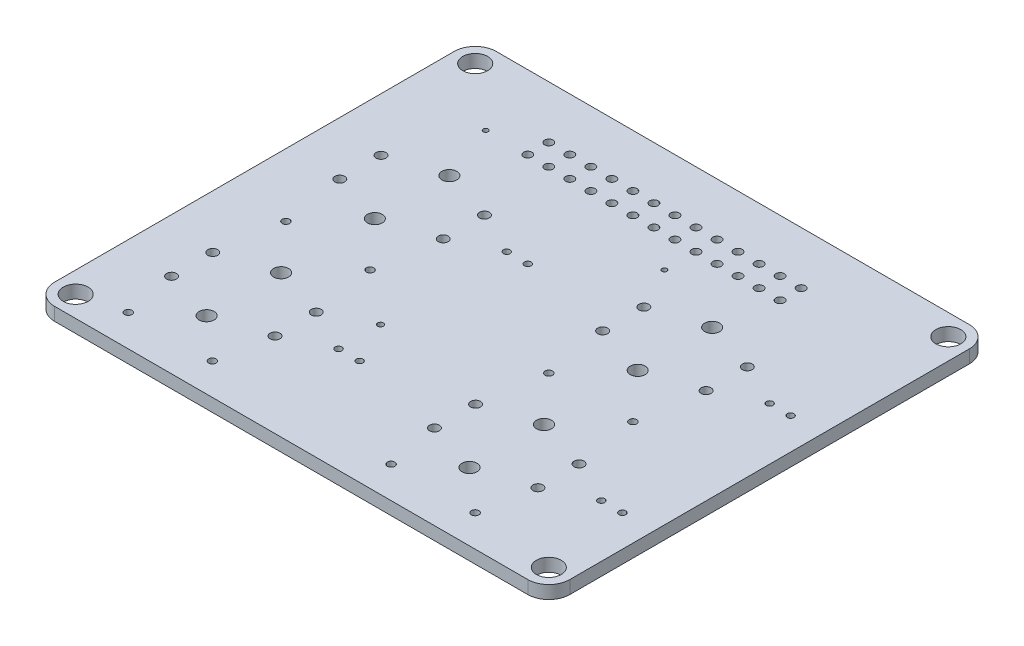
SolidWorks part; units mm, degrees
ref_plane "Front Plane" through (0, 0, 0) normal (0, 0, 1) x (1, 0, 0)
ref_plane "Top Plane" through (0, 0, 0) normal (0, 1, 0) x (1, 0, 0)
ref_plane "Right Plane" through (0, 0, 0) normal (1, 0, 0) x (0, 0, -1)
sketch "Sketch1" plane through (0, 0, 0) normal (0, 1, 0) x (1, 0, 0)
  line L1 (-28.575, 26.67) -> (28.575, 26.67)
  line L2 (-31.115, 24.13) -> (-31.115, -24.13)
  line L3 (-28.575, -26.67) -> (28.575, -26.67)
  line L4 (31.115, 24.13) -> (31.115, -24.13)
  line L5 (-31.115, 26.67) -> (31.115, -26.67) construction
  line L6 (-31.115, -26.67) -> (31.115, 26.67) construction
  arc A4 (28.575, 26.67) -> (31.115, 24.13) centre (28.575, 24.13) cw
  arc A5 (28.575, -26.67) -> (31.115, -24.13) centre (28.575, -24.13) ccw
  arc A6 (-31.115, -24.13) -> (-28.575, -26.67) centre (-28.575, -24.13) ccw
  arc A7 (-28.575, 26.67) -> (-31.115, 24.13) centre (-28.575, 24.13) ccw
  point P0 (0, 0)
  dimension "D15" = 2.54
  dimension "D1" = 62.23
  dimension "D2" = 53.34
extrude "Boss-Extrude1" add sketch "Sketch1" along normal blind 1.5748
sketch "Sketch2" plane through (0, 1.5748, 0) normal (0, 1, 0) x (1, 0, 0)
  line L0 (-28.575, 24.13) -> (-28.575, -24.13) construction
  line L1 (-28.575, -24.13) -> (28.575, -24.13) construction
  line L2 (28.575, -24.13) -> (28.575, 24.13) construction
  line L3 (28.575, 24.13) -> (-28.575, 24.13) construction
  line L4 (28.575, 26.67) -> (-28.575, 26.67) construction
  line L5 (-31.115, 24.13) -> (-31.115, -24.13) construction
  line L6 (31.115, -24.13) -> (31.115, 24.13) construction
  line L7 (-28.575, -26.67) -> (28.575, -26.67) construction
  line L8 (-24.6634, -11.4808) -> (-12.1666, -16.4592) construction
  line L9 (-24.6634, -16.4592) -> (-12.1666, -16.4592) construction
  line L10 (-24.6634, -16.4592) -> (-24.6634, -11.4808) construction
  line L11 (-24.6634, -11.4808) -> (-12.1666, -11.4808) construction
  line L12 (-12.1666, -16.4592) -> (-12.1666, -11.4808) construction
  line L13 (-12.1666, -11.4808) -> (-24.6634, -16.4592) construction
  line L14 (-18.415, -13.97) -> (-18.415, -22.86) construction
  line L15 (-13.335, -22.86) -> (-23.495, -22.86) construction
  line L16 (-18.415, -13.97) -> (-4.445, -13.97) construction
  line L17 (-18.415, -13.97) -> (-18.415, -9.4742) construction
  line L18 (7.0866, -11.4808) -> (19.5834, -16.4592) construction
  line L19 (7.0866, -16.4592) -> (19.5834, -16.4592) construction
  line L20 (7.0866, -16.4592) -> (7.0866, -11.4808) construction
  line L21 (7.0866, -11.4808) -> (19.5834, -11.4808) construction
  line L22 (19.5834, -16.4592) -> (19.5834, -11.4808) construction
  line L23 (19.5834, -11.4808) -> (7.0866, -16.4592) construction
  line L24 (13.335, -13.97) -> (13.335, -22.86) construction
  line L25 (13.335, -13.97) -> (27.305, -13.97) construction
  line L26 (13.335, -13.97) -> (13.335, -9.4742) construction
  line L27 (7.0866, 8.8392) -> (19.5834, 3.8608) construction
  line L28 (7.0866, 3.8608) -> (19.5834, 3.8608) construction
  line L29 (7.0866, 3.8608) -> (7.0866, 8.8392) construction
  line L30 (7.0866, 8.8392) -> (19.5834, 8.8392) construction
  line L31 (19.5834, 3.8608) -> (19.5834, 8.8392) construction
  line L32 (19.5834, 8.8392) -> (7.0866, 3.8608) construction
  line L33 (13.335, 6.35) -> (13.335, -2.54) construction
  line L34 (13.335, 6.35) -> (27.305, 6.35) construction
  line L35 (13.335, 6.35) -> (13.335, 10.8458) construction
  line L36 (-24.6634, 8.8392) -> (-12.1666, 3.8608) construction
  line L37 (-24.6634, 3.8608) -> (-12.1666, 3.8608) construction
  line L38 (-24.6634, 3.8608) -> (-24.6634, 8.8392) construction
  line L39 (-24.6634, 8.8392) -> (-12.1666, 8.8392) construction
  line L40 (-12.1666, 3.8608) -> (-12.1666, 8.8392) construction
  line L41 (-12.1666, 8.8392) -> (-24.6634, 3.8608) construction
  line L42 (-18.415, 6.35) -> (-18.415, -2.54) construction
  line L43 (-18.415, 6.35) -> (-4.445, 6.35) construction
  line L44 (-18.415, 6.35) -> (-18.415, 10.8458) construction
  line L45 (18.415, -22.86) -> (8.255, -22.86) construction
  line L46 (18.415, -3.81) -> (8.255, -3.81) construction
  line L47 (-13.335, -3.81) -> (-23.495, -3.81) construction
  circle A0 centre (-28.575, 24.13) radius 1.5
  circle A1 centre (28.575, 24.13) radius 1.5
  circle A2 centre (28.575, -24.13) radius 1.5
  circle A3 centre (-28.575, -24.13) radius 1.5
  circle A4 centre (-20.955, 17.78) radius 0.3
  circle A5 centre (14.605, 20.32) radius 0.508
  circle A6 centre (12.065, 20.32) radius 0.508
  circle A7 centre (9.525, 20.32) radius 0.508
  circle A8 centre (6.985, 20.32) radius 0.508
  circle A9 centre (4.445, 20.32) radius 0.508
  circle A10 centre (1.905, 20.32) radius 0.508
  circle A11 centre (-0.635, 20.32) radius 0.508
  circle A12 centre (-3.175, 20.32) radius 0.508
  circle A13 centre (-5.715, 20.32) radius 0.508
  circle A14 centre (-8.255, 20.32) radius 0.508
  circle A15 centre (-10.795, 20.32) radius 0.508
  circle A16 centre (-13.335, 20.32) radius 0.508
  circle A17 centre (-15.875, 20.32) radius 0.508
  circle A18 centre (12.065, 17.78) radius 0.508
  circle A19 centre (9.525, 17.78) radius 0.508
  circle A20 centre (6.985, 17.78) radius 0.508
  circle A21 centre (4.445, 17.78) radius 0.508
  circle A22 centre (1.905, 17.78) radius 0.508
  circle A23 centre (-0.635, 17.78) radius 0.508
  circle A24 centre (-3.175, 17.78) radius 0.508
  circle A25 centre (-5.715, 17.78) radius 0.508
  circle A26 centre (-8.255, 17.78) radius 0.508
  circle A27 centre (-10.795, 17.78) radius 0.508
  circle A28 centre (-13.335, 17.78) radius 0.508
  circle A29 centre (-15.875, 17.78) radius 0.508
  circle A30 centre (14.605, 17.78) radius 0.508
  circle A31 centre (4.445, 13.97) radius 0.3
  circle A32 centre (-24.6634, -11.4808) radius 0.5969
  circle A33 centre (-24.6634, -16.4592) radius 0.5969
  circle A34 centre (-12.1666, -16.4592) radius 0.5969
  circle A35 centre (-12.1666, -11.4808) radius 0.5969
  circle A36 centre (-23.495, -22.86) radius 0.45
  circle A37 centre (-13.335, -22.86) radius 0.45
  circle A38 centre (-6.985, -13.97) radius 0.4064
  circle A39 centre (-4.445, -13.97) radius 0.4064
  circle A40 centre (-18.415, -9.4742) radius 0.9017
  circle A41 centre (-18.415, -18.47) radius 0.9017
  circle A42 centre (7.0866, -11.4808) radius 0.5969
  circle A43 centre (7.0866, -16.4592) radius 0.5969
  circle A44 centre (19.5834, -16.4592) radius 0.5969
  circle A45 centre (19.5834, -11.4808) radius 0.5969
  circle A46 centre (24.765, -13.97) radius 0.4064
  circle A47 centre (27.305, -13.97) radius 0.4064
  circle A48 centre (13.335, -9.4742) radius 0.9017
  circle A49 centre (13.335, -18.47) radius 0.9017
  circle A50 centre (7.0866, 8.8392) radius 0.5969
  circle A51 centre (7.0866, 3.8608) radius 0.5969
  circle A52 centre (19.5834, 3.8608) radius 0.5969
  circle A53 centre (19.5834, 8.8392) radius 0.5969
  circle A54 centre (24.765, 6.35) radius 0.4064
  circle A55 centre (27.305, 6.35) radius 0.4064
  circle A56 centre (13.335, 10.8458) radius 0.9017
  circle A57 centre (13.335, 1.85) radius 0.9017
  circle A58 centre (-24.6634, 8.8392) radius 0.5969
  circle A59 centre (-24.6634, 3.8608) radius 0.5969
  circle A60 centre (-12.1666, 3.8608) radius 0.5969
  circle A61 centre (-12.1666, 8.8392) radius 0.5969
  circle A62 centre (-6.985, 6.35) radius 0.4064
  circle A63 centre (-4.445, 6.35) radius 0.4064
  circle A64 centre (-18.415, 10.8458) radius 0.9017
  circle A65 centre (-18.415, 1.85) radius 0.9017
  circle A66 centre (8.255, -22.86) radius 0.45
  circle A67 centre (18.415, -22.86) radius 0.45
  circle A68 centre (8.255, -3.81) radius 0.45
  circle A69 centre (18.415, -3.81) radius 0.45
  circle A70 centre (-23.495, -3.81) radius 0.45
  circle A71 centre (-13.335, -3.81) radius 0.45
  circle A72 centre (-6.985, -8.89) radius 0.35
  point P77 (-18.415, -13.97)
  point P89 (-5.715, -13.97)
  point P104 (13.335, -13.97)
  point P112 (26.035, -13.97)
  point P125 (13.335, 6.35)
  point P133 (26.035, 6.35)
  point P146 (-18.415, 6.35)
  point P154 (-5.715, 6.35)
  dimension "D5" = 3
  dimension "D6" = 3
  dimension "D7" = 3
  dimension "D8" = 3
  dimension "D9" = 0.6
  dimension "D12" = 1.016
  dimension "D17" = 0.6
  dimension "D22" = 1.1938
  dimension "D23" = 1.1938
  dimension "D24" = 1.1938
  dimension "D25" = 1.1938
  dimension "D30" = 0.9
  dimension "D31" = 0.9
  dimension "D35" = 0.8128
  dimension "D36" = 0.8128
  dimension "D37" = 1.8034
  dimension "D38" = 1.8034
  dimension "D41" = 0.7
  dimension "D1" = 2.54
  dimension "D2" = 2.54
  dimension "D3" = 2.54
  dimension "D4" = 2.54
  dimension "D10" = 10.16
  dimension "D11" = 4.4958
  dimension "D13" = 45.72
  dimension "D14" = 46.99
  dimension "D18" = 35.56
  dimension "D19" = 4.5
  dimension "D20" = 12.4968
  dimension "D21" = 4.9784
  dimension "D26" = 12.7
  dimension "D27" = 12.7
  dimension "D28" = 10.16
  dimension "D29" = 8.89
  dimension "D32" = 12.7
  dimension "D33" = 1.27
  dimension "D34" = 1.27
  dimension "D39" = 24.13
  dimension "D40" = 17.78
  dimension "D15" = 13
  dimension "D16" = 2
extrude "Cut-Extrude1" cut sketch "Sketch2" against normal through all
ref_point "Point2"
